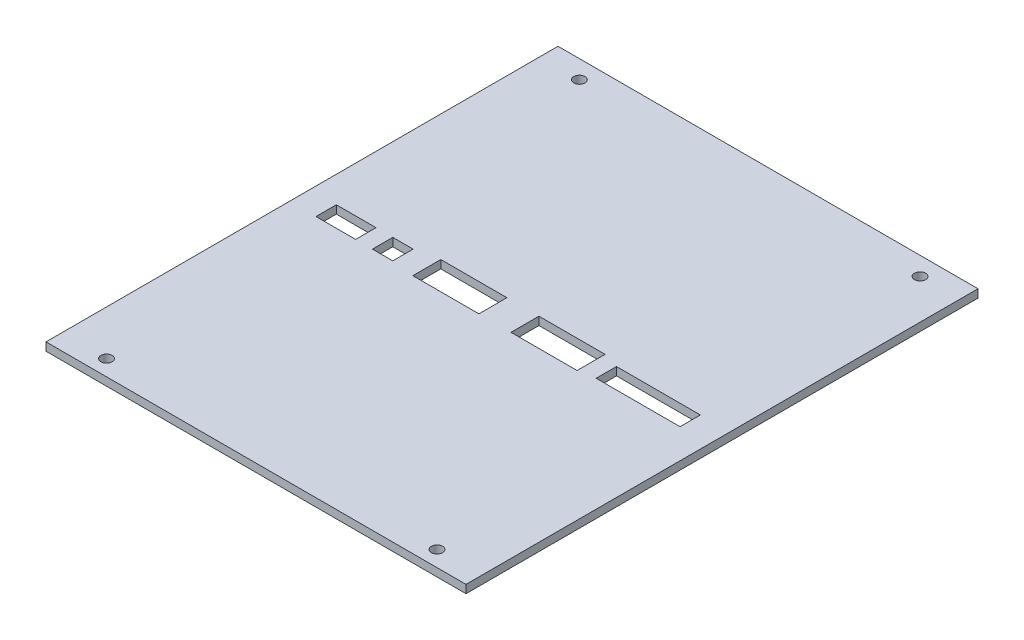
SolidWorks part; units mm, degrees
material "電力回路基板"
ref_plane "Front Plane" through (0, 0, 0) normal (0, 0, 1) x (1, 0, 0)
ref_plane "Top Plane" through (0, 0, 0) normal (0, 1, 0) x (1, 0, 0)
ref_plane "Right Plane" through (0, 0, 0) normal (1, 0, 0) x (0, 0, -1)
sketch "Sketch1" plane through (0, 0, 0) normal (0, 1, 0) x (1, 0, 0)
  line L0 (65.24, 0.2725) -> (65.24, -46.4375)
  line L1 (-17.76, 29.8625) -> (65.24, 29.8625)
  line L2 (65.24, 29.8625) -> (65.24, 21.5625)
  line L3 (-17.76, 4.3625) -> (-17.76, -45.7898)
  line L6 (65.24, -63.6375) -> (65.24, -70.1375)
  line L7 (65.24, -70.1375) -> (-17.76, -70.1375)
  line L8 (-17.76, -70.1375) -> (-17.76, -63.6375)
  line L11 (-17.76, 29.8625) -> (-17.76, 21.5625)
  line L17 (-17.76, -48.6375) -> (-17.76, -45.7898)
  line L21 (65.24, 6.5625) -> (65.24, 0.2725)
  line L22 (-17.76, 21.5625) -> (-17.76, 4.3625)
  line L23 (-17.76, -48.6375) -> (-17.76, -63.6375)
  line L24 (65.24, -46.4375) -> (65.24, -63.6375)
  line L25 (65.24, 6.5625) -> (65.24, 21.5625)
  dimension "D1" = 100
  dimension "D2" = 83
  dimension "D4" = 6.5
  dimension "D5" = 6.5
  dimension "D6" = 8.3
extrude "Boss-Extrude1" add sketch "Sketch1" along normal blind 1.6 contours L11 L22 L3 L17 L23 L8 L7 L6 L24 L0 L21 L25 L2 L1
sketch "Sketch3" plane through (0, 1.6, 0) normal (0, 1, 0) x (1, 0, 0)
  line L0 (65.24, 29.8625) -> (65.24, -70.1375) construction
  line L1 (7.24, -16.3875) -> (20.24, -16.3875)
  line L2 (7.24, -16.3875) -> (7.24, -21.8875)
  line L3 (7.24, -21.8875) -> (20.24, -21.8875)
  line L4 (20.24, -16.3875) -> (20.24, -21.8875)
  line L5 (42.74, -17.3375) -> (59.24, -17.3375)
  line L6 (42.74, -17.3375) -> (42.74, -21.3375)
  line L7 (42.74, -21.3375) -> (59.24, -21.3375)
  line L8 (59.24, -17.3375) -> (59.24, -21.3375)
  line L9 (-12.36, -17.3375) -> (-4.56, -17.3375)
  line L10 (-12.36, -17.3375) -> (-12.36, -21.3375)
  line L11 (-12.36, -21.3375) -> (-4.56, -21.3375)
  line L12 (-4.56, -17.3375) -> (-4.56, -21.3375)
  line L14 (-17.76, -19.1375) -> (65.24, -19.1375) construction
  line L15 (-17.76, -70.1375) -> (-17.76, 29.8625) construction
  line L16 (-17.76, 29.8625) -> (65.24, 29.8625) construction
  line L17 (26.54, -16.3875) -> (39.54, -16.3875)
  line L18 (26.54, -16.3875) -> (26.54, -21.8875)
  line L19 (26.54, -21.8875) -> (39.54, -21.8875)
  line L20 (39.54, -16.3875) -> (39.54, -21.8875)
  line L21 (-1.26, -17.3375) -> (2.74, -17.3375)
  line L22 (-1.26, -17.3375) -> (-1.26, -21.3375)
  line L23 (-1.26, -21.3375) -> (2.74, -21.3375)
  line L24 (2.74, -17.3375) -> (2.74, -21.3375)
  dimension "D2" = 7.8
  dimension "D3" = 4
  dimension "D4" = 4
  dimension "D5" = 5.5
  dimension "D6" = 1.8
  dimension "D7" = 13
  dimension "D8" = 1.8
  dimension "D9" = 2.75
  dimension "D10" = 11.8
  dimension "D11" = 16.5
  dimension "D12" = 6
  dimension "D13" = 49
  dimension "D14" = 6.3
  dimension "7.9" = 5.4
  dimension "D15" = 13
  dimension "D16" = 5.5
  dimension "D17" = 2.75
  dimension "D18" = 3.3
  dimension "D19" = 2.2
  dimension "D20" = 4
  dimension "D21" = 1.8
extrude "Cut-Extrude2" cut sketch "Sketch3" against normal blind 49
hole_wizard "Ø2.2 (2.2) Diameter Hole2" positions "Sketch6" profile "Sketch5" hole size "Ø2.2" standard "ANSI Metric"
sketch "Sketch6" plane through (0, 1.6, 0) normal (0, 1, 0) x (1, 0, 0)
  line L0 (-17.76, -70.1375) -> (-17.76, 29.8625) construction
  line L1 (65.24, 29.8625) -> (65.24, -70.1375) construction
  line L3 (65.24, -70.1375) -> (-17.76, -70.1375) construction
  point P30 (56.24, -66.1375)
  point P32 (-8.76, -66.1375)
  dimension "D1" = 4
  dimension "D2" = 9
  dimension "D7" = 9
  dimension "D8" = 4
sketch "Sketch5" plane through (56.24, 1.6, 66.1375) normal (1, 0, 0) x (0, 0, 1)
  line L0 (0, 0) -> (0, 5)
  line L1 (0, 5) -> (1.1, 5)
  line L2 (1.1, 5) -> (1.1, 0)
  line L5 (1.1, 0) -> (0, 0)
  line L10 (0, 5) -> (-1.1, 5) construction
  line L11 (0, -6.35) -> (0, 107.95) construction
  dimension "Hole Dia." = 2.2
  dimension "Hole Depth" = 5
  dimension "Drill Angle" = 180
sketch "Sketch12" plane through (0, 1.6, 0) normal (0, 1, 0) x (1, 0, 0)
  line L0 (65.24, 29.8625) -> (65.24, -70.1375) construction
  line L1 (-17.76, -70.1375) -> (65.24, -70.1375)
  line L2 (-17.76, -70.1375) -> (-17.76, -67.6375)
  line L3 (-17.76, -67.6375) -> (65.24, -67.6375)
  line L4 (65.24, -70.1375) -> (65.24, -67.6375)
  dimension "D1" = 2.5
extrude "Cut-Extrude4" cut sketch "Sketch12" against normal up to next
sketch "ｽｹｯﾁ1" plane through (0, 0, -29.8625) normal (0, 0, -1) x (-1, 0, 0)
  line L1 (-65.24, 1.6) -> (17.76, 1.6)
  line L2 (-65.24, 1.6) -> (-65.24, 0)
  line L3 (-65.24, 0) -> (17.76, 0)
  line L4 (17.76, 1.6) -> (17.76, 0)
extrude "ﾎﾞｽ - 押し出し1" add sketch "ｽｹｯﾁ1" along normal blind 1.6
sketch "ｽｹｯﾁ2" plane through (0, 0, 67.6375) normal (0, 0, 1) x (1, 0, 0)
  line L1 (-17.76, 1.6) -> (65.24, 1.6)
  line L2 (-17.76, 1.6) -> (-17.76, 0)
  line L3 (-17.76, 0) -> (65.24, 0)
  line L4 (65.24, 1.6) -> (65.24, 0)
extrude "ﾎﾞｽ - 押し出し2" add sketch "ｽｹｯﾁ2" along normal blind 1.6
sketch "Sketch13" plane through (0, 1.6, 0) normal (0, 1, 0) x (1, 0, 0)
  line L0 (-17.76, -69.2375) -> (-17.76, 31.4625) construction
  line L1 (65.24, 31.4625) -> (65.24, -69.2375) construction
  line L3 (-17.76, 31.4625) -> (65.24, 31.4625) construction
  point P0 (-9.76, 27.8625)
  point P1 (57.24, 27.8625)
  dimension "D1" = 8
  dimension "D2" = 8
  dimension "D3" = 3.6
  dimension "D4" = 3.6
hole_wizard "Ø2.2 (2.2) Diameter Hole1" positions "Sketch15" profile "Sketch14" hole size "Ø2.2" standard "Ansi Metric"
sketch "Sketch15" plane through (0, 1.6, 0) normal (0, 1, 0) x (1, 0, 0)
  point P0 (-9.76, 27.8625)
  point P3 (57.24, 27.8625)
sketch "Sketch14" plane through (-9.76, 1.6, -27.8625) normal (1, 0, 0) x (0, 0, 1)
  line L0 (0, 0) -> (0, 1.6)
  line L1 (0, 1.6) -> (1.1, 1.6)
  line L2 (1.1, 1.6) -> (1.1, 0)
  line L5 (1.1, 0) -> (0, 0)
  line L10 (0, 1.6) -> (-1.1, 1.6) construction
  line L11 (0, -6.35) -> (0, 107.95) construction
  dimension "穴の直径" = 2.2
  dimension "穴の深さ" = 1.6
  dimension "ﾄﾞﾘﾙ角度" = 180
sketch "Sketch16" plane through (0, 1.6, 0) normal (0, 1, 0) x (1, 0, 0)
  line L0 (65.24, -69.2375) -> (-17.76, -69.2375) construction
  line L1 (-17.76, 31.4625) -> (-17.56, 31.4625)
  line L2 (-17.76, 31.4625) -> (-17.76, -69.2375)
  line L3 (-17.76, -69.2375) -> (-17.56, -69.2375)
  line L4 (-17.56, 31.4625) -> (-17.56, -69.2375)
  line L5 (-17.76, 31.4625) -> (65.24, 31.4625) construction
  line L6 (65.24, -69.2375) -> (65.04, -69.2375)
  line L7 (65.24, -69.2375) -> (65.24, 31.4625)
  line L8 (65.24, 31.4625) -> (65.04, 31.4625)
  line L9 (65.04, -69.2375) -> (65.04, 31.4625)
  dimension "D1" = 0.2
  dimension "D2" = 0.2
extrude "Extrude1" cut sketch "Sketch16" against normal through all
